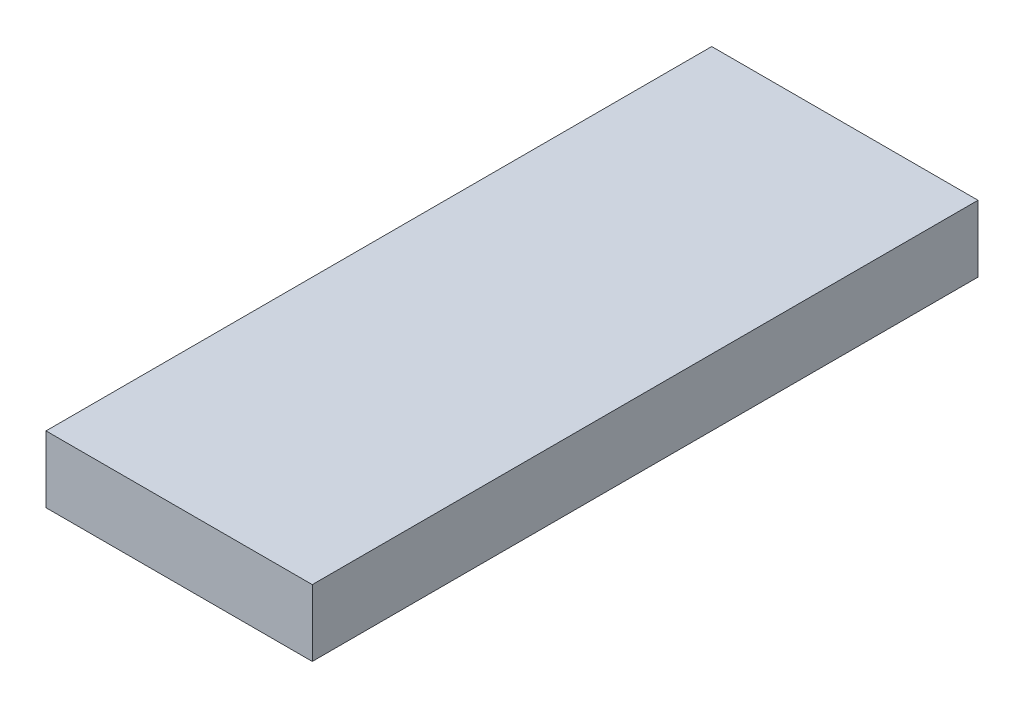
SolidWorks part; units mm, degrees
ref_plane "Front Plane" through (0, 0, 0) normal (0, 0, 1) x (1, 0, 0)
ref_plane "Top Plane" through (0, 0, 0) normal (0, 1, 0) x (1, 0, 0)
ref_plane "Right Plane" through (0, 0, 0) normal (1, 0, 0) x (0, 0, -1)
sketch "Sketch1" plane through (0, 0, 0) normal (0, 1, 0) x (1, 0, 0)
  line L1 (0, 0) -> (20, 0)
  line L2 (0, 0) -> (0, 50)
  line L3 (0, 50) -> (20, 50)
  line L4 (20, 0) -> (20, 50)
  dimension "D1" = 20
  dimension "D2" = 50
extrude "Boss-Extrude1" add sketch "Sketch1" along normal blind 5
